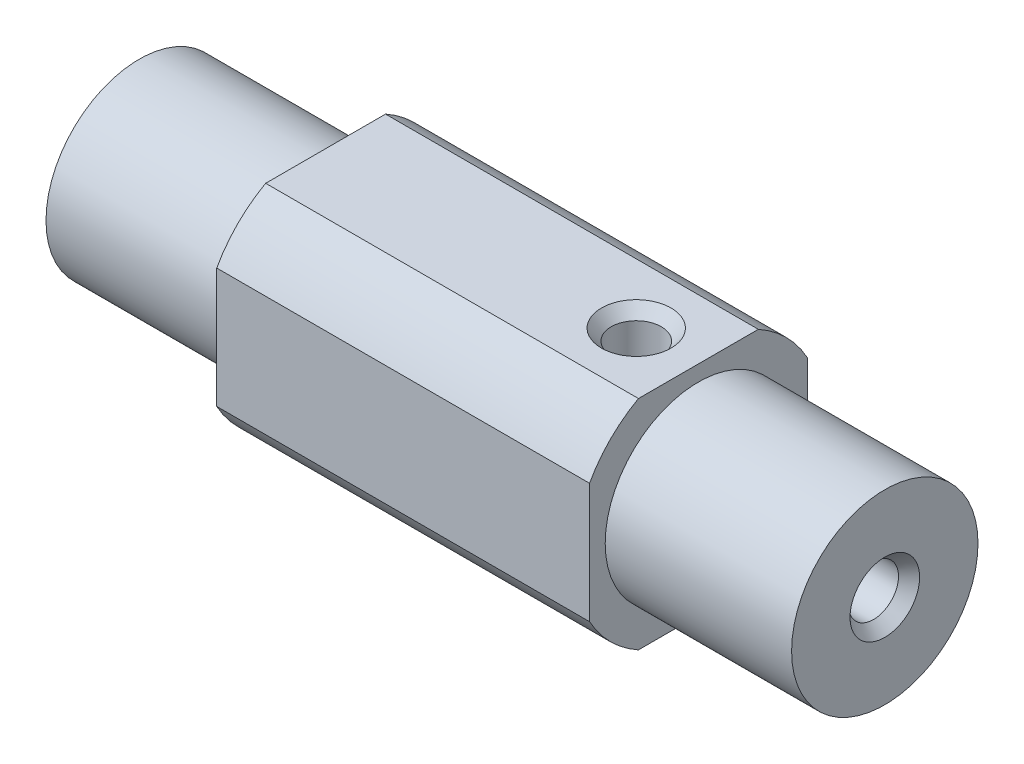
SolidWorks part; units mm, degrees
material "6061-T6 (SS)"
ref_plane "Front Plane" through (0, 0, 0) normal (0, 0, 1) x (1, 0, 0)
ref_plane "Top Plane" through (0, 0, 0) normal (0, 1, 0) x (1, 0, 0)
ref_plane "Right Plane" through (0, 0, 0) normal (1, 0, 0) x (0, 0, -1)
sketch "Sketch1" plane through (0, 0, 0) normal (1, 0, 0) x (0, 0, -1)
  circle A0 centre (0, 0) radius 12.7
extrude "Boss-Extrude1" add sketch "Sketch1" against normal blind 79.375
sketch "Sketch2" plane through (0, 0, 0) normal (1, 0, 0) x (0, 0, -1)
  circle A0 centre (0, 0) radius 9.525
  circle A1 centre (0, 0) radius 21.2934
extrude "Cut-Extrude1" cut sketch "Sketch2" against normal blind 19.05
ref_plane "Plane1" through (0, 0, 11.1252) normal (0, 0, 1) x (1, 0, 0)
sketch "Sketch3" plane through (0, 12.4012, 11.1252) normal (0, 0, 1) x (1, 0, 0)
  line L1 (-91.2436, 24.1614) -> (-2.896, 24.1614)
  line L2 (-91.2436, 24.1614) -> (-91.2436, -37.9233)
  line L3 (-91.2436, -37.9233) -> (-2.896, -37.9233)
  line L4 (-2.896, 24.1614) -> (-2.896, -37.9233)
extrude "Cut-Extrude2" cut sketch "Sketch3" along normal blind 7.62
ref_plane "Plane3" through (0, 11.1252, 0) normal (0, 1, 0) x (-1, 0, 0)
sketch "Sketch7" plane through (0, 11.1252, 0) normal (0, 1, 0) x (-1, 0, 0)
  line L1 (96.4133, -27.0383) -> (-22.4115, -27.0383)
  line L2 (96.4133, -27.0383) -> (96.4133, 24.8097)
  line L3 (96.4133, 24.8097) -> (-22.4115, 24.8097)
  line L4 (-22.4115, -27.0383) -> (-22.4115, 24.8097)
extrude "Cut-Extrude5" cut sketch "Sketch7" along normal blind 25.4
hole_wizard "1/4-20 Tapped Hole2" positions "Sketch15" profile "Sketch14" tap size "1/4-20" standard "Ansi Inch"
sketch "Sketch15" plane through (0, 11.1252, 0) normal (0, 1, 0) x (-1, 0, 0)
  line L0 (0, 13.1039) -> (0, -13.1039) construction
  line L1 (13.1039, 11.1252) -> (-13.1039, 11.1252) construction
  point P0 (25.4, 0)
  dimension "D1" = 25.4
  dimension "D2" = 11.1252
cosmetic thread "Hole Thread2" parameters "D1"=12.7, "D2"=6.35
sketch "Sketch14" plane through (-25.4, 11.1252, 0) normal (1, 0, 0) x (0, 0, 1)
  line L0 (0, 0) -> (0, 17.5358)
  line L1 (0, 17.5358) -> (2.5527, 16.002)
  line L2 (2.5527, 16.002) -> (2.5527, 1.1542)
  line L3 (2.5527, 1.1542) -> (3.556, 0)
  line L5 (3.556, 0) -> (0, 0)
  line L6 (-2.5527, 1.1542) -> (-3.556, 0) construction
  line L10 (0, 17.5358) -> (-2.5527, 16.002) construction
  line L11 (0, -6.35) -> (0, 107.95) construction
  dimension "Tap Drill Dia." = 5.1054
  dimension "Tap Drill Depth" = 16.002
  dimension "Near C'Sink Dia." = 7.112
  dimension "Near C'Sink Angle" = 82
  dimension "Drill Angle" = 118
cosmetic thread "Cosmetic Thread1" parameters "D1"=5, "D2"=6.35
hole_wizard "1/4-20 Tapped Hole3" positions "Sketch17" profile "Sketch16" tap size "1/4-20" standard "Ansi Inch"
sketch "Sketch17" plane through (0, 0, 0) normal (1, 0, 0) x (0, 0, -1)
  point P0 (0, 0)
sketch "Sketch16" plane through (0, 0, 0) normal (0, 1, 0) x (0, 0, -1)
  line L0 (0, 0) -> (0, 17.5358)
  line L1 (0, 17.5358) -> (2.5527, 16.002)
  line L2 (2.5527, 16.002) -> (2.5527, 1.1542)
  line L3 (2.5527, 1.1542) -> (3.556, 0)
  line L5 (3.556, 0) -> (0, 0)
  line L6 (-2.5527, 1.1542) -> (-3.556, 0) construction
  line L10 (0, 17.5358) -> (-2.5527, 16.002) construction
  line L11 (0, -6.35) -> (0, 107.95) construction
  dimension "Tap Drill Dia." = 5.1054
  dimension "Tap Drill Depth" = 16.002
  dimension "Near C'Sink Dia." = 7.112
  dimension "Near C'Sink Angle" = 82
  dimension "Drill Angle" = 118
cosmetic thread "Hole Thread3" parameters "D1"=12.7, "D2"=6.35
sketch "Sketch18" plane through (-79.375, 0, 0) normal (-1, 0, 0) x (0, 0, 1)
  circle A0 centre (0, 0) radius 21.6882
  circle A1 centre (0, 0) radius 9.525
  circle A2 centre (0, 0) radius 21.6882
sketch "Sketch26" plane through (0, 0, 0) normal (1, 0, 0) x (0, 0, -1)
  line L1 (-14.1212, -11.1252) -> (11.1252, -11.1252)
  line L2 (-14.1212, -11.1252) -> (-14.1212, -15.7963)
  line L3 (-14.1212, -15.7963) -> (15.19, -15.7963)
  line L4 (15.19, -11.6283) -> (15.19, -15.7963)
  line L5 (11.1252, 12.0776) -> (19.4943, 12.0776)
  line L6 (11.1252, 12.0776) -> (11.1252, -11.1252)
  line L7 (15.19, -11.6283) -> (19.4943, -11.6283)
  line L8 (19.4943, 12.0776) -> (19.4943, -11.6283)
  dimension "D1" = 11.1252
  dimension "D2" = 11.1252
extrude "Cut-Extrude10" cut sketch "Sketch26" against normal blind 88.9
extrude "Cut-Extrude12" cut sketch "Sketch18" against normal blind 3.175 contours A0
sketch "Sketch30" plane through (-76.2, 0, 0) normal (-1, 0, 0) x (0, 0, 1)
  circle A0 centre (0, 0) radius 17.8473
  circle A1 centre (0, 0) radius 9.525
extrude "Cut-Extrude13" cut sketch "Sketch30" against normal blind 19.05
hole_wizard "1/4-20 Tapped Hole6" positions "Sketch32" profile "Sketch31" tap size "1/4-20" standard "Ansi Inch"
sketch "Sketch32" plane through (-76.2, 0, 0) normal (-1, 0, 0) x (0, 0, 1)
  point P0 (0, 0)
sketch "Sketch31" plane through (-76.2, 0, 0) normal (0, 1, 0) x (0, 0, 1)
  line L0 (0, 0) -> (0, 17.5358)
  line L1 (0, 17.5358) -> (2.5527, 16.002)
  line L2 (2.5527, 16.002) -> (2.5527, 1.1542)
  line L3 (2.5527, 1.1542) -> (3.556, 0)
  line L5 (3.556, 0) -> (0, 0)
  line L6 (-2.5527, 1.1542) -> (-3.556, 0) construction
  line L10 (0, 17.5358) -> (-2.5527, 16.002) construction
  line L11 (0, -6.35) -> (0, 107.95) construction
  dimension "Tap Drill Dia." = 5.1054
  dimension "Tap Drill Depth" = 16.002
  dimension "Near C'Sink Dia." = 7.112
  dimension "Near C'Sink Angle" = 82
  dimension "Drill Angle" = 118
cosmetic thread "Hole Thread6" parameters "D1"=12.7, "D2"=6.35
hole_wizard "1/4-20 Tapped Hole7" positions "Sketch36" profile "Sketch35" tap size "1/4-20" standard "Ansi Inch"
sketch "Sketch36" plane through (0, -11.1252, 0) normal (0, -1, 0) x (1, 0, 0)
  line L0 (0, -9.525) -> (0, 9.525) construction
  line L1 (-19.05, -11.1252) -> (-57.15, -11.1252) construction
  point P0 (-50.8, 0)
  dimension "D1" = 50.8
  dimension "D2" = 11.1252
sketch "Sketch35" plane through (-50.8, -11.1252, 0) normal (1, 0, 0) x (0, 0, -1)
  line L0 (0, 0) -> (0, 17.5358)
  line L1 (0, 17.5358) -> (2.5527, 16.002)
  line L2 (2.5527, 16.002) -> (2.5527, 1.1542)
  line L3 (2.5527, 1.1542) -> (3.556, 0)
  line L5 (3.556, 0) -> (0, 0)
  line L6 (-2.5527, 1.1542) -> (-3.556, 0) construction
  line L10 (0, 17.5358) -> (-2.5527, 16.002) construction
  line L11 (0, -6.35) -> (0, 107.95) construction
  dimension "Tap Drill Dia." = 5.1054
  dimension "Tap Drill Depth" = 16.002
  dimension "Near C'Sink Dia." = 7.112
  dimension "Near C'Sink Angle" = 82
  dimension "Drill Angle" = 118
cosmetic thread "Hole Thread7" parameters "D1"=12.7, "D2"=6.35
